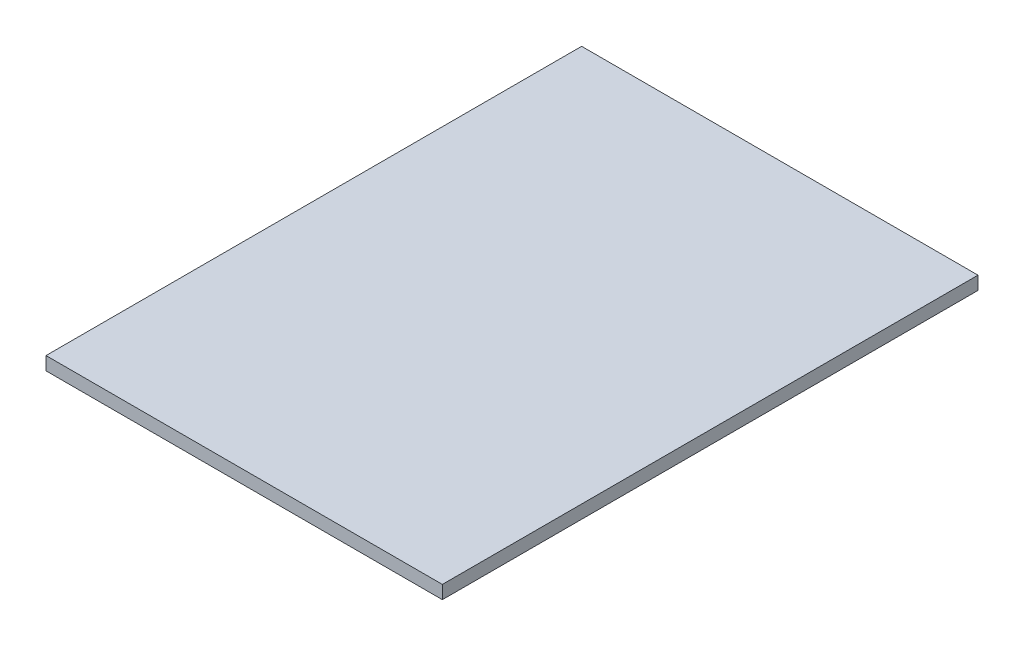
SolidWorks part; units mm, degrees
ref_plane "Front Plane" through (0, 0, 0) normal (0, 0, 1) x (1, 0, 0)
ref_plane "Top Plane" through (0, 0, 0) normal (0, 1, 0) x (1, 0, 0)
ref_plane "Right Plane" through (0, 0, 0) normal (1, 0, 0) x (0, 0, -1)
sketch "Sketch1" plane through (0, 0, 0) normal (0, 1, 0) x (1, 0, 0)
  line L1 (-178.562, -241.3) -> (178.562, -241.3)
  line L2 (-178.562, -241.3) -> (-178.562, 241.3)
  line L3 (-178.562, 241.3) -> (178.562, 241.3)
  line L4 (178.562, -241.3) -> (178.562, 241.3)
  line L5 (-178.562, -241.3) -> (178.562, 241.3) construction
  line L6 (-178.562, 241.3) -> (178.562, -241.3) construction
  point P0 (0, 0)
  dimension "D1" = 357.124
  dimension "D2" = 482.6
extrude "Boss-Extrude1" add sketch "Sketch1" along normal blind 11.938
